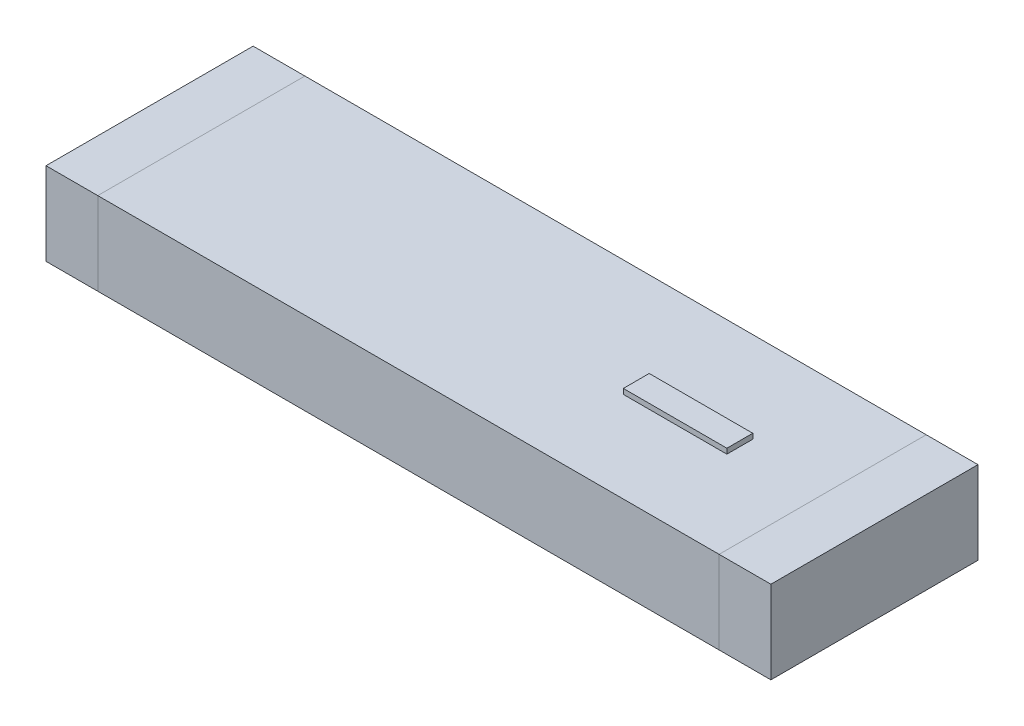
SolidWorks part; units mm, degrees
ref_plane "Front Plane" through (0, 0, 0) normal (0, 0, 1) x (1, 0, 0)
ref_plane "Top Plane" through (0, 0, 0) normal (0, 1, 0) x (1, 0, 0)
ref_plane "Right Plane" through (0, 0, 0) normal (1, 0, 0) x (0, 0, -1)
sketch "Sketch2" plane through (0, 0, 0) normal (0, 1, 0) x (1, 0, 0)
  line L1 (-3, -1) -> (3, -1)
  line L2 (-3, -1) -> (-3, 1)
  line L3 (-3, 1) -> (3, 1)
  line L4 (3, -1) -> (3, 1)
  line L5 (-3, -1) -> (3, 1) construction
  line L6 (-3, 1) -> (3, -1) construction
  point P0 (0, 0)
  point P6 (-3.5, 1.3509)
  dimension "D1" = 6
  dimension "D2" = 2
extrude "Boss-Extrude1" add sketch "Sketch2" along normal blind 0.8
sketch "Sketch3" plane through (0, 0, 0) normal (0, 1, 0) x (1, 0, 0)
  line L0 (0, 1) -> (0, -1) construction
  line L1 (-3, 1) -> (-3.5, 1)
  line L2 (-3, 1) -> (-3, -1)
  line L3 (-3, -1) -> (-3.5, -1)
  line L4 (-3.5, 1) -> (-3.5, -1)
  line L5 (3, 1) -> (-3, 1) construction
  line L6 (-3, -1) -> (3, -1) construction
  line L7 (3, -1) -> (3.5, -1)
  line L8 (3.5, 1) -> (3.5, -1)
  line L9 (3, 1) -> (3.5, 1)
  line L10 (3, 1) -> (3, -1)
  dimension "D1" = 2
  dimension "D2" = 0.5
extrude "Boss-Extrude2" add sketch "Sketch3" along normal blind 0.8 separate body
sketch "Sketch4" plane through (0, 0.8, 0) normal (0, 1, 0) x (1, 0, 0)
  line L0 (0, 0) -> (3, 0) construction
  line L4 (3, 1) -> (3, -1) construction
  line L6 (1.2, -0.125) -> (2.2, -0.125)
  line L7 (1.2, -0.125) -> (1.2, 0.125)
  line L8 (1.2, 0.125) -> (2.2, 0.125)
  line L9 (2.2, -0.125) -> (2.2, 0.125)
  line L10 (1.2, -0.125) -> (2.2, 0.125) construction
  line L11 (1.2, 0.125) -> (2.2, -0.125) construction
  point P4 (1.7, 0)
  dimension "D1" = 0.8
  dimension "D2" = 0.25
  dimension "D3" = 1
extrude "Boss-Extrude3" add sketch "Sketch4" against normal blind 0.1 from offset 0.05 separate body
